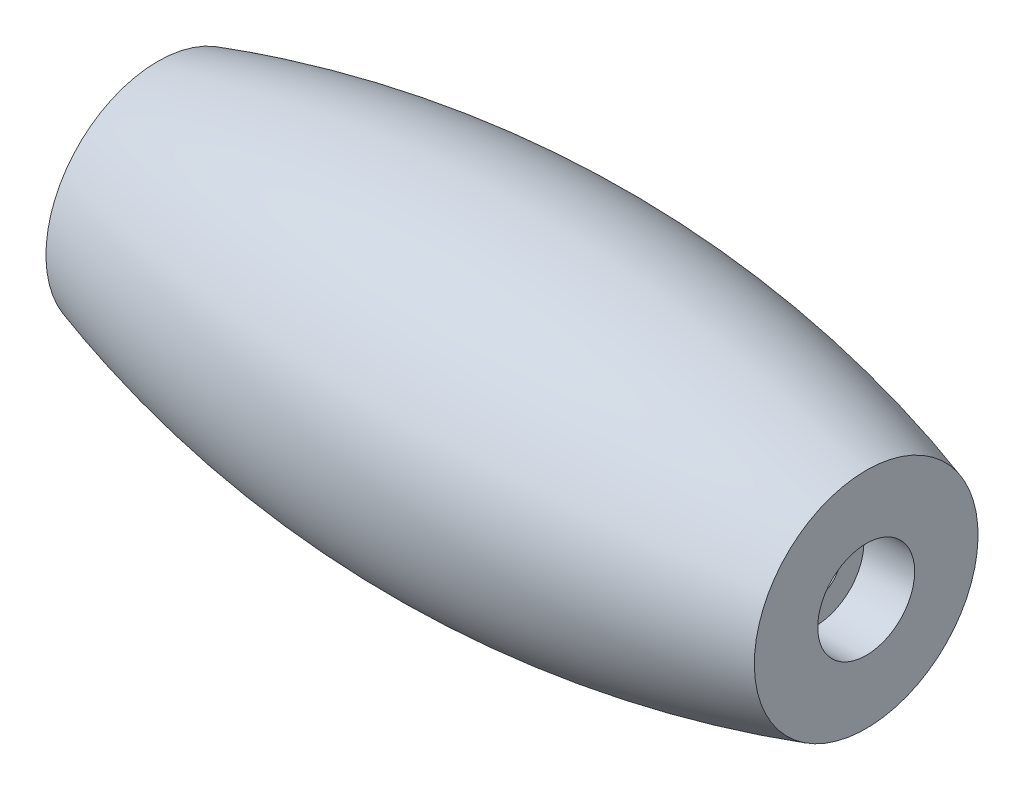
SolidWorks part; units mm, degrees
material "PTFE (general)"
ref_plane "Front Plane" through (0, 0, 0) normal (0, 0, 1) x (1, 0, 0)
ref_plane "Top Plane" through (0, 0, 0) normal (0, 1, 0) x (1, 0, 0)
ref_plane "Right Plane" through (0, 0, 0) normal (1, 0, 0) x (0, 0, -1)
sketch "Sketch1" plane through (0, 0, 0) normal (0, 0, 1) x (1, 0, 0)
  line L0 (0, 0) -> (0, 7.5)
  line L1 (47.5, 7.5) -> (47.5, 0)
  line L2 (47.5, 0) -> (0, 0)
  arc A0 (0, 7.5) -> (47.5, 7.5) centre (23.75, -68.8933) cw
  dimension "D3" = 80
  dimension "D1" = 7.5
  dimension "D2" = 47.5
revolve "Revolve1" add sketch "Sketch1" angle 360 about L2
hole_wizard "CBORE for M3 Hex Socket Head Cap Screw1" positions "Sketch2" profile "Sketch4" counterbore size "M3" standard "DIN"
sketch "Sketch2" plane through (47.5, 0, 0) normal (1, 0, 0) x (0, 0, -1)
  point P0 (0, 0)
sketch "Sketch4" plane through (47.5, 0, 0) normal (0, 1, 0) x (0, 0, -1)
  line L0 (0, 0) -> (0, 12.5915)
  line L1 (0, 12.5915) -> (1.7, 11.57)
  line L2 (1.7, 11.57) -> (1.7, 3.4)
  line L3 (1.7, 3.4) -> (3.25, 3.4)
  line L4 (3.25, 3.4) -> (3.25, 0)
  line L5 (3.25, 0) -> (0, 0)
  line L10 (0, 12.5915) -> (-1.7, 11.57) construction
  line L11 (0, -6.35) -> (0, 107.95) construction
  dimension "Hole Dia." = 3.4
  dimension "Hole Depth" = 11.57
  dimension "C'Bore Dia." = 6.5
  dimension "C'Bore Depth" = 3.4
  dimension "Drill Angle" = 118
hole_wizard "CBORE for M3 Hex Socket Head Cap Screw2" positions "Sketch5" profile "Sketch6" counterbore size "M3" standard "DIN"
sketch "Sketch5" plane through (0, 0, 0) normal (-1, 0, 0) x (0, 0, 1)
  point P0 (0, 0)
sketch "Sketch6" plane through (0, 0, 0) normal (0, 1, 0) x (0, 0, 1)
  line L0 (0, 0) -> (0, 12.5915)
  line L1 (0, 12.5915) -> (1.7, 11.57)
  line L2 (1.7, 11.57) -> (1.7, 3.4)
  line L3 (1.7, 3.4) -> (3.25, 3.4)
  line L4 (3.25, 3.4) -> (3.25, 0)
  line L5 (3.25, 0) -> (0, 0)
  line L10 (0, 12.5915) -> (-1.7, 11.57) construction
  line L11 (0, -6.35) -> (0, 107.95) construction
  dimension "Hole Dia." = 3.4
  dimension "Hole Depth" = 11.57
  dimension "C'Bore Dia." = 6.5
  dimension "C'Bore Depth" = 3.4
  dimension "Drill Angle" = 118
